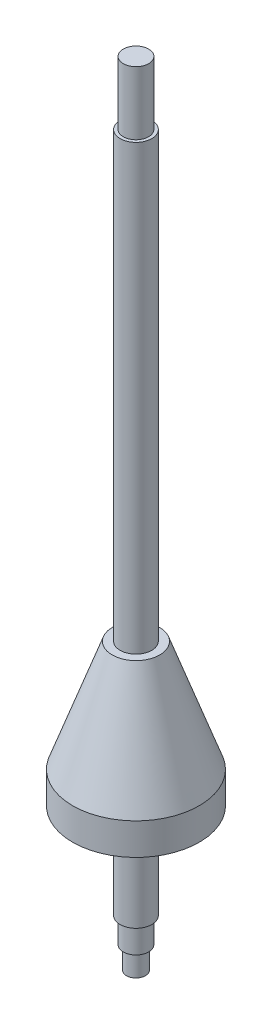
SolidWorks part; units mm, degrees
ref_plane "Front Plane" through (0, 0, 0) normal (0, 0, 1) x (1, 0, 0)
ref_plane "Top Plane" through (0, 0, 0) normal (0, 1, 0) x (1, 0, 0)
ref_plane "Right Plane" through (0, 0, 0) normal (1, 0, 0) x (0, 0, -1)
sketch "Sketch1" plane through (0, 0, 0) normal (0, 0, 1) x (1, 0, 0)
  line L0 (0, 266.5797) -> (0, -187.3551) construction
  line L1 (10, 0) -> (20, 0)
  line L2 (20, 0) -> (20, 10)
  line L3 (20, 10) -> (7.5, 45)
  line L4 (7.5, 45) -> (5, 45)
  line L5 (5, 45) -> (5, 185)
  line L6 (5, 185) -> (4, 185)
  line L7 (4, 185) -> (4, 205)
  line L8 (4, 205) -> (0, 205)
  line L9 (10, 0) -> (10, -5)
  line L10 (10, -5) -> (5, -5)
  line L11 (5, -5) -> (5, -30)
  line L12 (5, -30) -> (4, -30)
  line L13 (4, -30) -> (4, -38)
  line L14 (4, -38) -> (3, -38)
  line L15 (3, -38) -> (3, -45)
  line L16 (3, -45) -> (0, -45)
  line L17 (0, -45) -> (0, 205)
  dimension "D1" = 8
  dimension "D2" = 10
  dimension "D3" = 15
  dimension "D4" = 40
  dimension "D5" = 20
  dimension "D6" = 10
  dimension "D7" = 8
  dimension "D8" = 6
  dimension "D9" = 10
  dimension "D10" = 45
  dimension "D11" = 185
  dimension "D12" = 20
  dimension "D13" = 5
  dimension "D14" = 30
  dimension "D15" = 38
  dimension "D16" = 45
revolve "Revolve3" add sketch "Sketch1" angle 360 about L0
